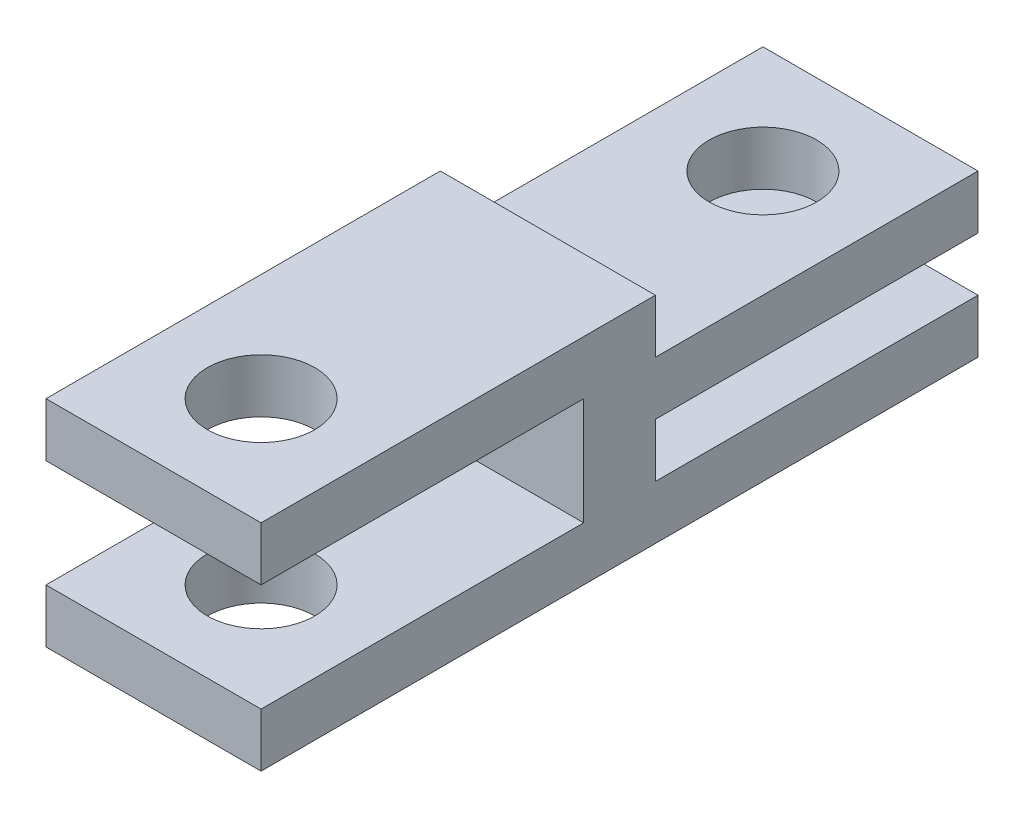
SolidWorks part; units mm, degrees
ref_plane "Front Plane" through (0, 0, 0) normal (0, 0, 1) x (1, 0, 0)
ref_plane "Top Plane" through (0, 0, 0) normal (0, 1, 0) x (1, 0, 0)
ref_plane "Right Plane" through (0, 0, 0) normal (1, 0, 0) x (0, 0, -1)
sketch "Sketch1" plane through (0, 0, 0) normal (1, 0, 0) x (0, 0, -1)
  line L12 (0, 0) -> (-20, 0)
  line L13 (-20, 0) -> (-20, 1.5)
  line L14 (-20, 1.5) -> (-11, 1.5)
  line L15 (-11, 1.5) -> (-11, 4.5)
  line L16 (-11, 4.5) -> (-20, 4.5)
  line L17 (-20, 4.5) -> (-20, 6)
  line L18 (-20, 6) -> (-9, 6)
  line L19 (-9, 6) -> (-9, 4.5)
  line L20 (-9, 4.5) -> (0, 4.5)
  line L21 (0, 4.5) -> (0, 3)
  line L22 (0, 3) -> (-9, 3)
  line L23 (-9, 3) -> (-9, 1.5)
  line L24 (-9, 1.5) -> (0, 1.5)
  line L25 (0, 1.5) -> (0, 0)
  point P25 (-9, 3.0658)
  dimension "D5" = 20
  dimension "D6" = 9
  dimension "D7" = 3
  dimension "D8" = 1.5
  dimension "D9" = 1.5
  dimension "D10" = 1.5
  dimension "D11" = 1.5
  dimension "D12" = 1.5
extrude "Boss-Extrude1" add sketch "Sketch1" along normal blind 6
sketch "Sketch2" plane through (0, 0, 0) normal (0, -1, 0) x (1, 0, 0)
  line L0 (0, 3) -> (6, 3) construction
  line L1 (0, 20) -> (0, 0) construction
  line L2 (6, 20) -> (6, 0) construction
  line L3 (0, 17) -> (6, 17) construction
  line L4 (6, 0) -> (0, 0) construction
  line L5 (6, 20) -> (0, 20) construction
  circle A0 centre (3, 3) radius 1.5
  circle A1 centre (3, 17) radius 1.5
  point P12 (4.354, 3.9631)
  point P13 (3, 3)
  point P14 (4.0509, 16.2844)
  point P15 (3, 17)
  dimension "D1" = 3
  dimension "D2" = 3
  dimension "D3" = 3
  dimension "D4" = 3
extrude "Cut-Extrude1" cut sketch "Sketch2" against normal blind 6
